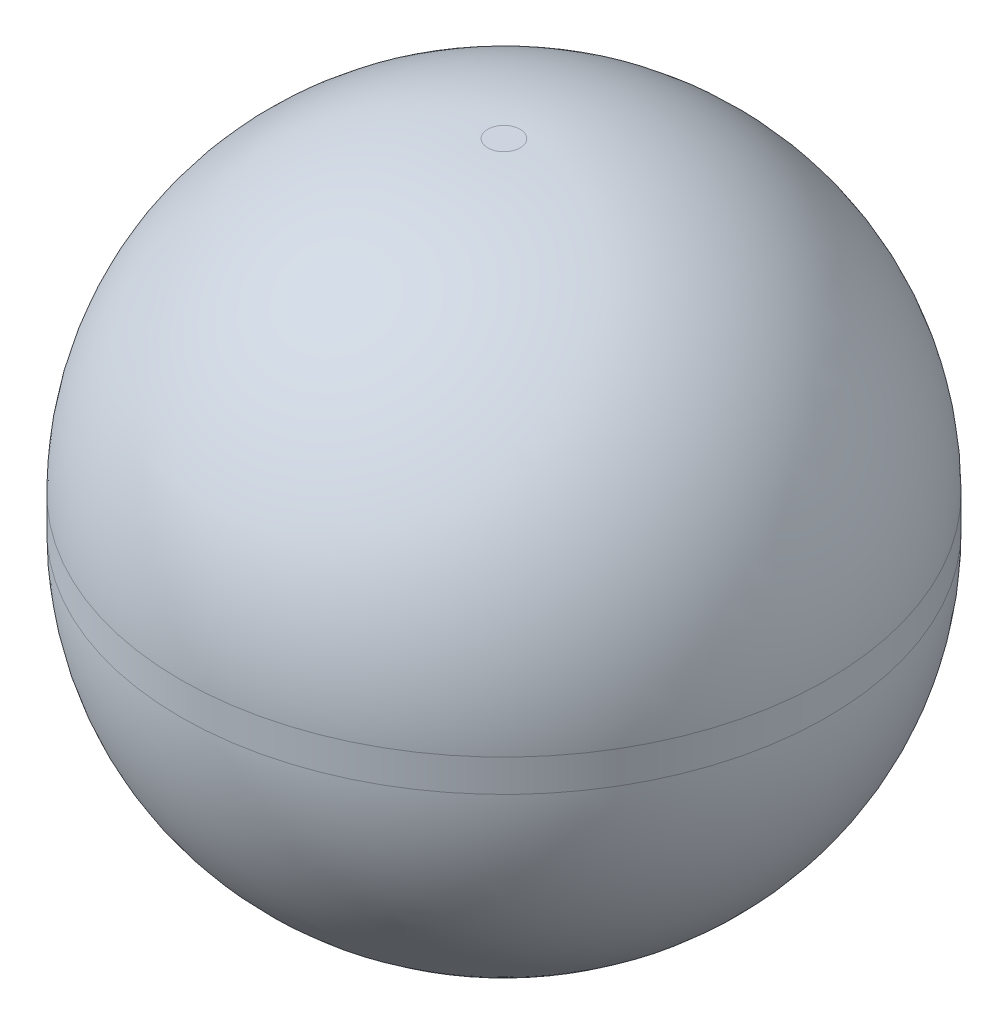
SolidWorks part; units mm, degrees
ref_plane "Plan de face" through (0, 0, 0) normal (0, 0, 1) x (1, 0, 0)
ref_plane "Plan de dessus" through (0, 0, 0) normal (0, 1, 0) x (1, 0, 0)
ref_plane "Plan de droite" through (0, 0, 0) normal (1, 0, 0) x (0, 0, -1)
sketch "Esquisse1" plane through (0, 0, 0) normal (0, 1, 0) x (1, 0, 0)
  circle A0 centre (0, 0) radius 20
  dimension "D1" = 40
extrude "Extrusion1" add sketch "Esquisse1" along normal blind 40
fillet "Congé1" radius 19 2 edges at (0, 0, 20) (0, 40, 20)
